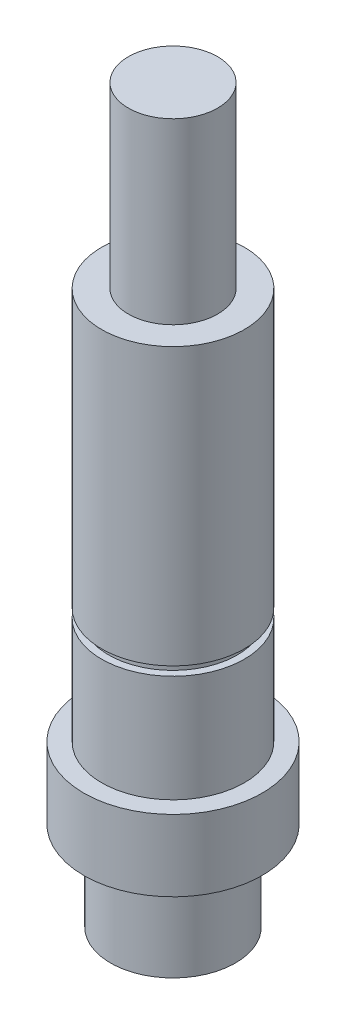
SolidWorks part; units mm, degrees
material "Nylon 101"
ref_plane "Front Plane" through (0, 0, 0) normal (0, 0, 1) x (1, 0, 0)
ref_plane "Top Plane" through (0, 0, 0) normal (0, 1, 0) x (1, 0, 0)
ref_plane "Right Plane" through (0, 0, 0) normal (1, 0, 0) x (0, 0, -1)
sketch "Sketch2" plane through (0, 0, 0) normal (0, 0, 1) x (1, 0, 0)
  line L0 (-2.4452, 34.1954) -> (-2.4452, 24.1954)
  line L1 (-2.4452, 24.1954) -> (-3.9452, 24.1954)
  line L2 (-3.9452, 24.1954) -> (-3.9452, 8.6954)
  line L3 (-3.9452, 2.1954) -> (-4.9452, 2.1954)
  line L4 (-4.9452, 2.1954) -> (-4.9452, -1.8046)
  line L5 (-4.9452, -1.8046) -> (-3.4452, -1.8046)
  line L6 (-3.4452, -1.8046) -> (-3.4452, -6.8046)
  line L7 (-3.4452, -6.8046) -> (0.0548, -6.8046)
  line L8 (0.0548, -6.8046) -> (0.0548, 34.1954) construction
  line L9 (-2.4452, 34.1954) -> (0.0548, 34.1954)
  line L10 (0.0548, -6.8046) -> (0.0548, 34.1954)
  line L11 (-3.9452, 8.1954) -> (-3.5452, 8.1954)
  line L12 (-3.5452, 8.1954) -> (-3.5452, 8.6954)
  line L13 (-3.5452, 8.6954) -> (-3.9452, 8.6954)
  line L14 (-3.9452, 8.1954) -> (-3.9452, 2.1954)
  dimension "D1" = 4
  dimension "D2" = 3.5
  dimension "D3" = 5
  dimension "D4" = 4
  dimension "D5" = 5
  dimension "D6" = 10
  dimension "D7" = 22
  dimension "D8" = 2.5
  dimension "D9" = 0.4
  dimension "D10" = 0.5
  dimension "D11" = 6
revolve "Revolve1" add sketch "Sketch2" angle 360 about L8
